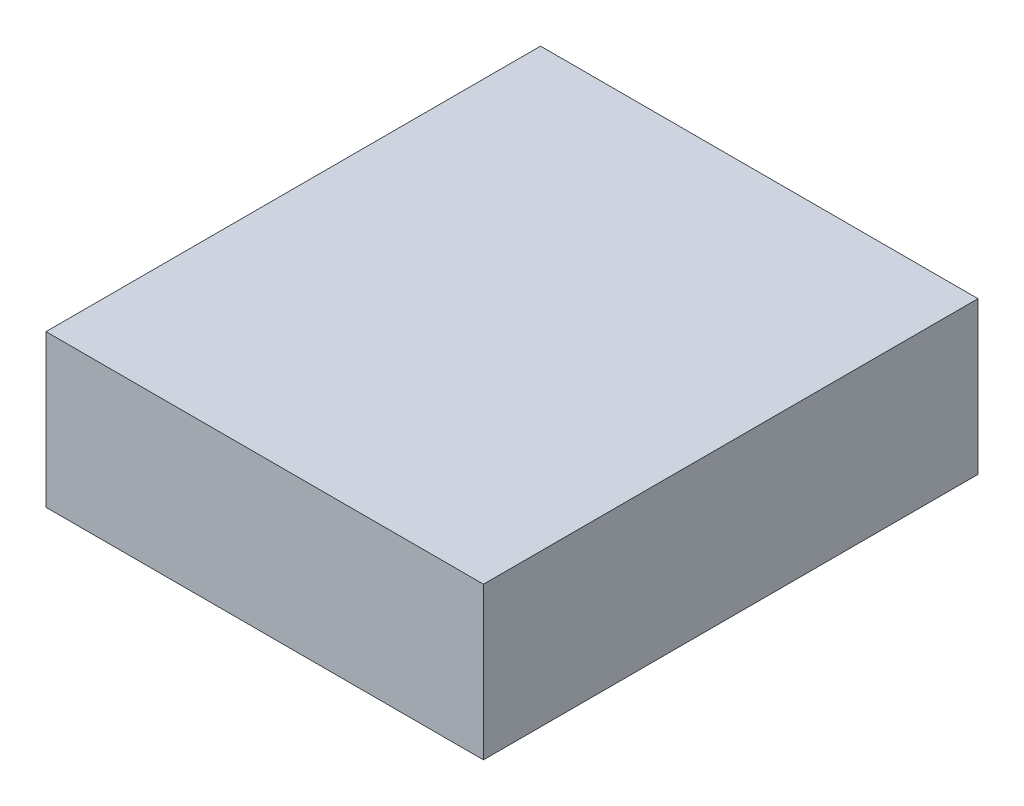
SolidWorks part; units mm, degrees
material "Nylon 6/10"
ref_plane "Plan de face" through (0, 0, 0) normal (0, 0, 1) x (1, 0, 0)
ref_plane "Plan de dessus" through (0, 0, 0) normal (0, 1, 0) x (1, 0, 0)
ref_plane "Plan de droite" through (0, 0, 0) normal (1, 0, 0) x (0, 0, -1)
sketch "Esquisse2" plane through (0, 0, 0) normal (0, 1, 0) x (1, 0, 0)
  line L1 (0, 0) -> (23, 0)
  line L2 (0, 0) -> (0, 26)
  line L3 (0, 26) -> (23, 26)
  line L4 (23, 0) -> (23, 26)
  dimension "D1" = 26
  dimension "D2" = 23
extrude "Extrusion1" add sketch "Esquisse2" along normal blind 8
